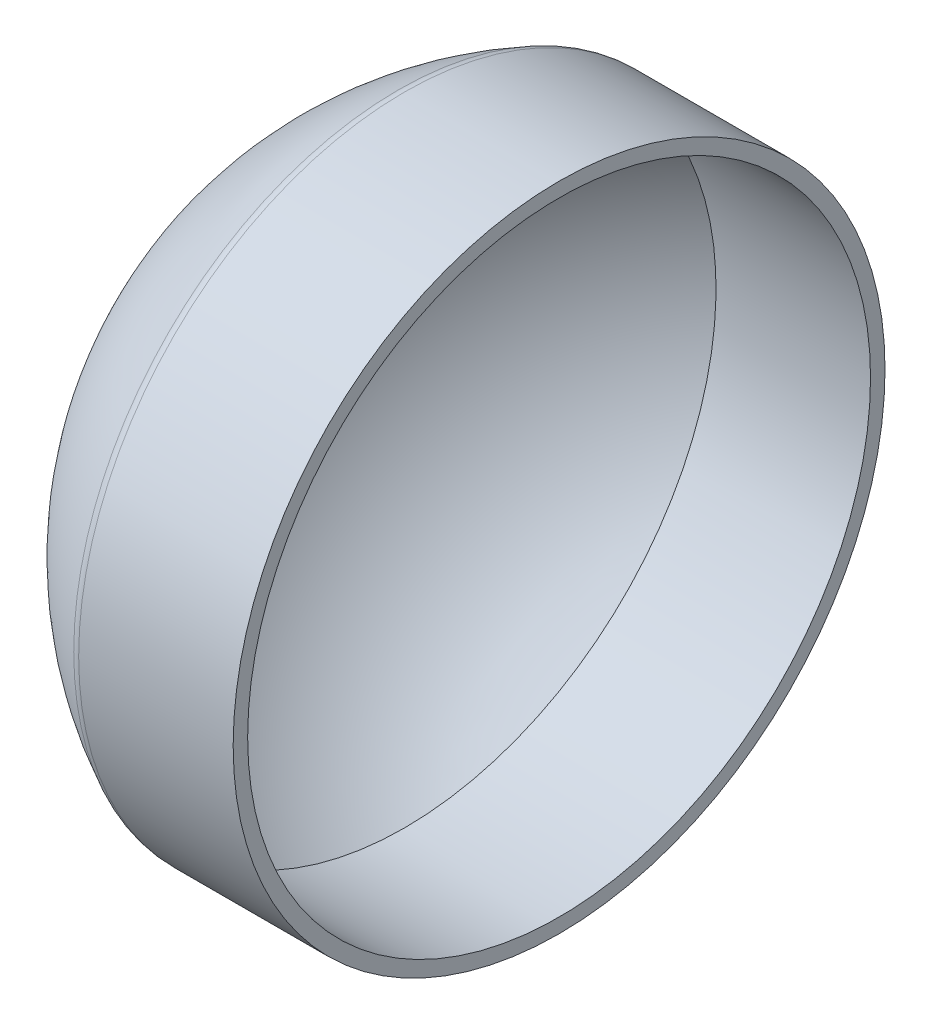
SolidWorks part; units mm, degrees
material "AISI 304"
ref_plane "Front Plane" through (0, 0, 0) normal (0, 0, 1) x (1, 0, 0)
ref_plane "Top Plane" through (0, 0, 0) normal (0, 1, 0) x (1, 0, 0)
ref_plane "Right Plane" through (0, 0, 0) normal (1, 0, 0) x (0, 0, -1)
sketch "Sketch1" plane through (0, 0, 0) normal (0, 0, 1) x (1, 0, 0)
  line L0 (-317.5006, 0) -> (317.5006, 0) construction
  line L1 (317.5006, 0) -> (317.5006, 571.5011) construction
  line L2 (317.5006, 571.5011) -> (40.71, 571.5011)
  line L3 (317.5006, 571.5011) -> (317.5006, 546.1011)
  line L4 (317.5006, 546.1011) -> (46.5998, 546.1011)
  line L5 (-317.5006, 0) -> (-292.1006, 0)
  arc A0 (40.71, 571.5011) -> (-317.5006, 0) centre (317.5006, 0) ccw
  arc A1 (46.5998, 546.1011) -> (-292.1006, 0) centre (317.5006, 0) ccw
  point P3 (0, 0)
  dimension "D1" = 635.0013
  dimension "D2" = 1143.0023
  dimension "D3" = 25.4001
  dimension "Thickness" = 25.4001
revolve "Revolve3" add sketch "Sketch1" angle 360 about L5
fillet "Fillet1" radius 25.4 1 edges at (40.71, 0, 571.5011)
